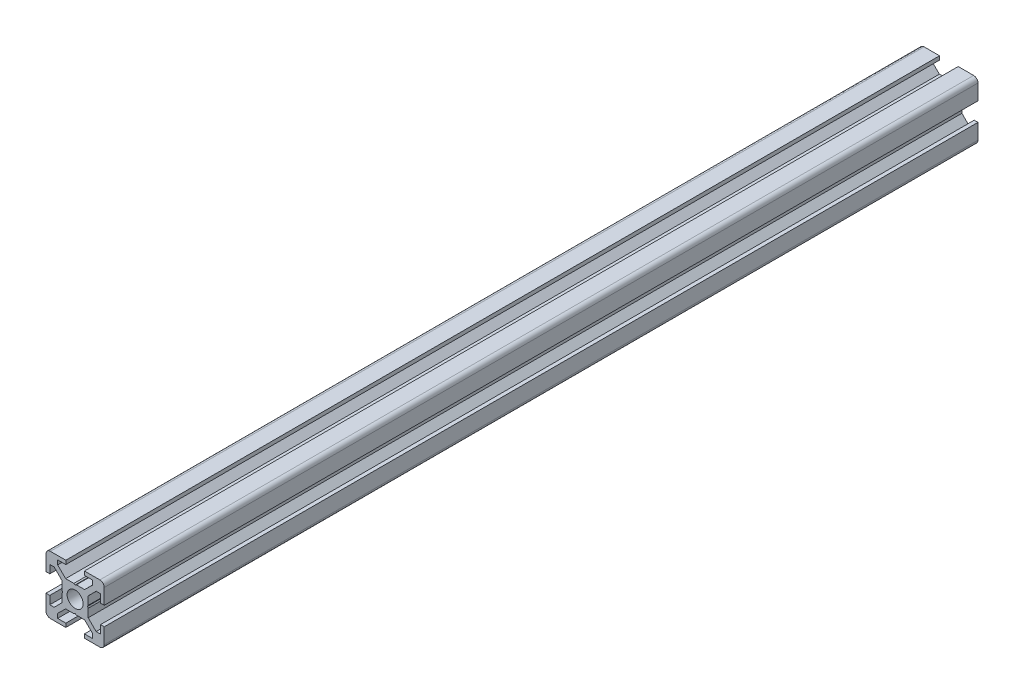
SolidWorks part; units mm, degrees
ref_plane "Front Plane" through (0, 0, 0) normal (0, 0, 1) x (1, 0, 0)
ref_plane "Top Plane" through (0, 0, 0) normal (0, 1, 0) x (1, 0, 0)
ref_plane "Right Plane" through (0, 0, 0) normal (1, 0, 0) x (0, 0, -1)
sketch "Model" plane through (0, 0, 0) normal (0, 0, 1) x (1, 0, 0)
  line L0 (1.5, 20) -> (6.8, 20)
  line L1 (6.8, 20) -> (6.8, 18.7)
  line L2 (6.8, 18.7) -> (4, 18.7)
  line L3 (4, 18.7) -> (4, 17.2)
  line L4 (4, 17.2) -> (6.7458, 14.5)
  line L5 (5.5, 13.2542) -> (5.5, 10.4348)
  line L6 (13.2542, 14.5) -> (16, 17.2)
  line L7 (16, 17.2) -> (16, 18.7)
  line L8 (16, 18.7) -> (13.2, 18.7)
  line L9 (13.2, 18.7) -> (13.2, 20)
  line L10 (13.2, 20) -> (18.5, 20)
  line L11 (20, 18.5) -> (20, 13.2)
  line L12 (20, 13.2) -> (18.7, 13.2)
  line L13 (18.7, 13.2) -> (18.7, 16)
  line L14 (18.7, 16) -> (17.2, 16)
  line L15 (17.2, 16) -> (14.5, 13.2542)
  line L17 (14.5, 6.7458) -> (17.2, 4)
  line L18 (17.2, 4) -> (18.7, 4)
  line L19 (18.7, 4) -> (18.7, 6.8)
  line L20 (18.7, 6.8) -> (20, 6.8)
  line L21 (20, 6.8) -> (20, 1.5)
  line L22 (18.5, 0) -> (13.2, 0)
  line L23 (13.2, 0) -> (13.2, 1.3)
  line L24 (13.2, 1.3) -> (16, 1.3)
  line L25 (16, 1.3) -> (16, 2.7987)
  line L26 (16, 2.7987) -> (13.2541, 5.5)
  line L27 (6.7458, 5.5) -> (9.5652, 5.5)
  line L28 (6.7458, 5.5) -> (4, 2.8)
  line L29 (4, 2.8) -> (4, 1.3)
  line L30 (4, 1.3) -> (6.8, 1.3)
  line L31 (6.8, 1.3) -> (6.8, 0)
  line L32 (6.8, 0) -> (1.5, 0)
  line L33 (0, 1.5) -> (0, 6.8)
  line L34 (0, 6.8) -> (1.3, 6.8)
  line L35 (1.3, 6.8) -> (1.3, 4)
  line L36 (1.3, 4) -> (2.8, 4)
  line L37 (2.8, 4) -> (5.5, 6.7458)
  line L39 (5.5, 13.2542) -> (2.8, 16)
  line L40 (2.8, 16) -> (1.3, 16)
  line L41 (1.3, 16) -> (1.3, 13.2)
  line L42 (1.3, 13.2) -> (0, 13.2)
  line L43 (0, 13.2) -> (0, 18.5)
  line L44 (14.5, 9.5652) -> (14.5, 6.7458)
  line L45 (10.4348, 14.5) -> (13.2542, 14.5)
  line L46 (10, 5.75) -> (9.5652, 5.5)
  line L47 (10, 5.75) -> (10.4348, 5.5)
  line L48 (10.4348, 5.5) -> (13.2541, 5.5)
  line L49 (10, 14.25) -> (10.4348, 14.5)
  line L50 (10, 14.25) -> (9.5652, 14.5)
  line L51 (6.7458, 14.5) -> (9.5652, 14.5)
  line L52 (5.5, 10.4348) -> (5.75, 10)
  line L53 (5.5, 9.5652) -> (5.75, 10)
  line L54 (5.5, 9.5652) -> (5.5, 6.7458)
  line L55 (14.5, 9.5652) -> (14.25, 10)
  line L56 (14.5, 10.4348) -> (14.25, 10)
  line L57 (14.5, 13.2542) -> (14.5, 10.4348)
  circle A0 centre (10, 10) radius 2.75
  arc A1 (18.5, 20) -> (20, 18.5) centre (18.5, 18.5) cw
  arc A2 (20, 1.5) -> (18.5, 0) centre (18.5, 1.5) cw
  arc A3 (1.5, 0) -> (0, 1.5) centre (1.5, 1.5) cw
  arc A4 (0, 18.5) -> (1.5, 20) centre (1.5, 18.5) cw
  dimension "D1" = 1.5
  dimension "D2" = 5.5
  dimension "D4" = 6.4
  dimension "D5" = 12
other "AlignGroup1"
extrude "Boss-Extrude1" add sketch "Model" along normal blind 300
